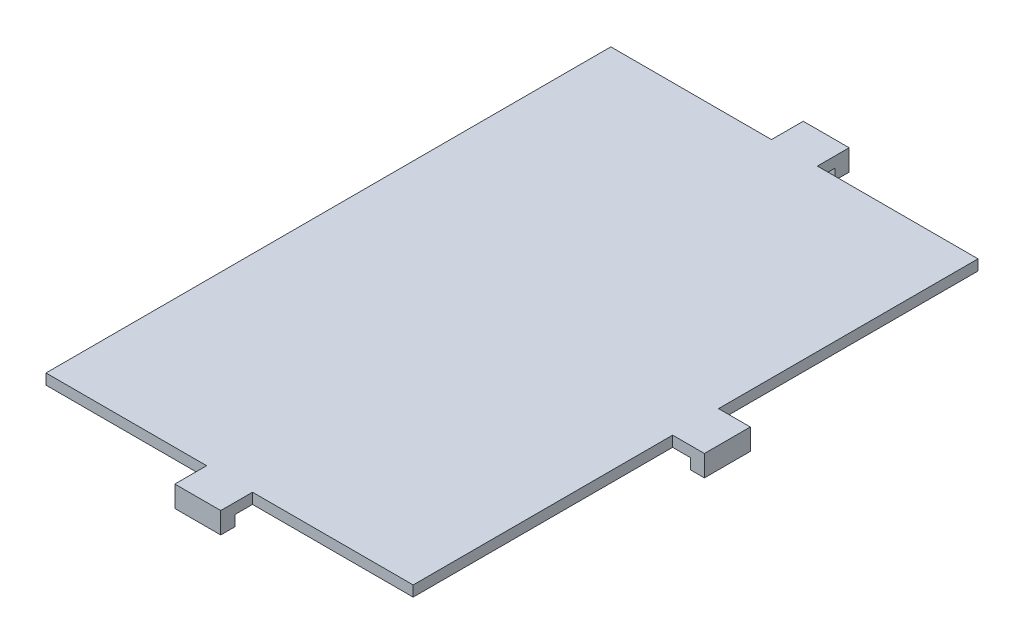
SolidWorks part; units mm, degrees
ref_plane "Front Plane" through (0, 0, 0) normal (0, 0, 1) x (1, 0, 0)
ref_plane "Top Plane" through (0, 0, 0) normal (0, 1, 0) x (1, 0, 0)
ref_plane "Right Plane" through (0, 0, 0) normal (1, 0, 0) x (0, 0, -1)
sketch "Sketch1" plane through (0, 0, 0) normal (0, 1, 0) x (1, 0, 0)
  line L0 (30, 81) -> (53, 81)
  line L1 (0, 0) -> (23, 0)
  line L2 (0, 0) -> (0, 81)
  line L3 (0, 81) -> (23, 81)
  line L4 (53, 0) -> (53, 37)
  line L6 (23, 0) -> (23, -2)
  line L7 (23, -2) -> (30, -2)
  line L8 (30, 0) -> (30, -2)
  line L11 (23, 83) -> (30, 83)
  line L12 (23, 83) -> (23, 81)
  line L14 (30, 83) -> (30, 81)
  line L15 (53, 44) -> (53, 81)
  line L16 (30, 0) -> (53, 0)
  line L17 (53, 44) -> (55, 44)
  line L19 (53, 37) -> (55, 37)
  line L20 (55, 44) -> (55, 37)
  point P5 (26.5, 0)
  point P10 (26.5, 81)
  point P15 (53, 40.5)
  dimension "D1" = 81
  dimension "D2" = 53
  dimension "D3" = 2
  dimension "D4" = 7
  dimension "D5" = 7
  dimension "D6" = 2
  dimension "D7" = 7
  dimension "D8" = 2
extrude "Boss-Extrude1" add sketch "Sketch1" along normal blind 1.5
sketch "Sketch2" plane through (0, 1.5, 0) normal (0, 1, 0) x (1, 0, 0)
  line L2 (23, 83) -> (30, 83)
  line L3 (23, 83) -> (23, 85)
  line L4 (23, 85) -> (30, 85)
  line L5 (30, 83) -> (30, 85)
  line L6 (55, 44) -> (57, 44)
  line L7 (55, 44) -> (55, 37)
  line L8 (55, 37) -> (57, 37)
  line L9 (57, 44) -> (57, 37)
  line L10 (23, -2) -> (30, -2)
  line L11 (23, -2) -> (23, -4)
  line L12 (23, -4) -> (30, -4)
  line L13 (30, -2) -> (30, -4)
  dimension "D1" = 7
  dimension "D2" = 7
  dimension "D3" = 7
  dimension "D4" = 2
  dimension "D5" = 2
  dimension "D6" = 2
extrude "Boss-Extrude2" add sketch "Sketch2" against normal blind 3
sketch "Sketch3" plane through (0, 1.5, 0) normal (0, 1, 0) x (1, 0, 0)
  line L0 (0, 80.5) -> (23, 80.5)
  line L1 (0, 81) -> (0, 0) construction
  line L2 (53, 44) -> (53, 81) construction
  line L3 (23, 81) -> (0, 81) construction
  line L4 (23, 81) -> (23, 80.5)
  line L5 (30, 81) -> (30, 80.5)
  line L6 (0, 80.5) -> (0, 81)
  line L7 (0, 81) -> (23, 81)
  line L8 (30, 81) -> (53, 81)
  line L9 (53, 81) -> (53, 80.5)
  line L10 (30, 80.5) -> (53, 80.5)
  dimension "D1" = 0.5
extrude "Cut-Extrude1" cut sketch "Sketch3" against normal blind 10
sketch "Sketch4" plane through (0, 1.5, 0) normal (0, 1, 0) x (1, 0, 0)
  line L0 (53, 0) -> (53, 37) construction
  line L1 (0, 0) -> (23, 0)
  line L2 (0, 0) -> (0, 0.5)
  line L3 (0, 0.5) -> (23, 0.5)
  line L4 (53, 0) -> (53, 0.5)
  line L5 (23, 0) -> (23, 0.5)
  line L6 (23, 0) -> (23, -4) construction
  line L7 (30, 0) -> (30, 0.5)
  line L8 (30, 0.5) -> (53, 0.5)
  line L9 (30, 0) -> (53, 0)
  dimension "D1" = 0.5
extrude "Cut-Extrude2" cut sketch "Sketch4" against normal blind 10
sketch "Sketch5" plane through (0, 1.5, 0) normal (0, 1, 0) x (1, 0, 0)
  line L0 (30, 85) -> (23, 85) construction
  line L1 (23, 80.5) -> (23.25, 80.5)
  line L2 (23, 80.5) -> (23, 85)
  line L3 (23, 85) -> (23.25, 85)
  line L4 (23.25, 80.5) -> (23.25, 85)
  line L5 (57, 37) -> (57, 44) construction
  line L6 (30, 80.5) -> (29.75, 80.5)
  line L7 (30, 80.5) -> (30, 85)
  line L8 (30, 85) -> (29.75, 85)
  line L9 (29.75, 80.5) -> (29.75, 85)
  line L10 (53, 44) -> (57, 44)
  line L11 (53, 44) -> (53, 43.75)
  line L12 (53, 43.75) -> (57, 43.75)
  line L13 (57, 44) -> (57, 43.75)
  line L14 (23, -4) -> (30, -4) construction
  line L15 (53, 37) -> (57, 37)
  line L16 (53, 37) -> (53, 37.25)
  line L17 (53, 37.25) -> (57, 37.25)
  line L18 (57, 37) -> (57, 37.25)
  line L19 (23, 0.5) -> (23.25, 0.5)
  line L20 (23, 0.5) -> (23, -4)
  line L21 (23, -4) -> (23.25, -4)
  line L22 (23.25, 0.5) -> (23.25, -4)
  line L24 (30, -4) -> (29.75, -4)
  line L25 (30, -4) -> (30, 0.5)
  line L26 (30, 0.5) -> (29.75, 0.5)
  line L27 (29.75, -4) -> (29.75, 0.5)
  dimension "D1" = 0.25
  dimension "D2" = 0.25
  dimension "D3" = 0.25
  dimension "D4" = 0.25
  dimension "D5" = 0.25
  dimension "D6" = 0.25
extrude "Cut-Extrude3" cut sketch "Sketch5" against normal blind 10
sketch "Sketch6" plane through (0, 1.5, 0) normal (0, 1, 0) x (1, 0, 0)
  line L0 (23.25, 0.5) -> (0, 0.5) construction
  line L1 (0, 80.5) -> (0.5, 80.5)
  line L2 (0, 80.5) -> (0, 0.5)
  line L3 (0, 0.5) -> (0.5, 0.5)
  line L4 (0.5, 80.5) -> (0.5, 0.5)
  line L5 (29.75, 80.5) -> (53, 80.5) construction
  line L6 (53, 0.5) -> (52.5, 0.5)
  line L7 (53, 0.5) -> (53, 37.25)
  line L8 (53, 80.5) -> (52.5, 80.5)
  line L9 (52.5, 0.5) -> (52.5, 37.25)
  line L10 (53, 43.75) -> (53, 80.5)
  line L11 (53, 43.75) -> (52.5, 43.75)
  line L13 (53, 37.25) -> (52.5, 37.25)
  line L15 (52.5, 43.75) -> (52.5, 80.5)
  dimension "D1" = 0.5
  dimension "D2" = 0.5
  dimension "D3" = 0.5
extrude "Cut-Extrude4" cut sketch "Sketch6" against normal blind 10
